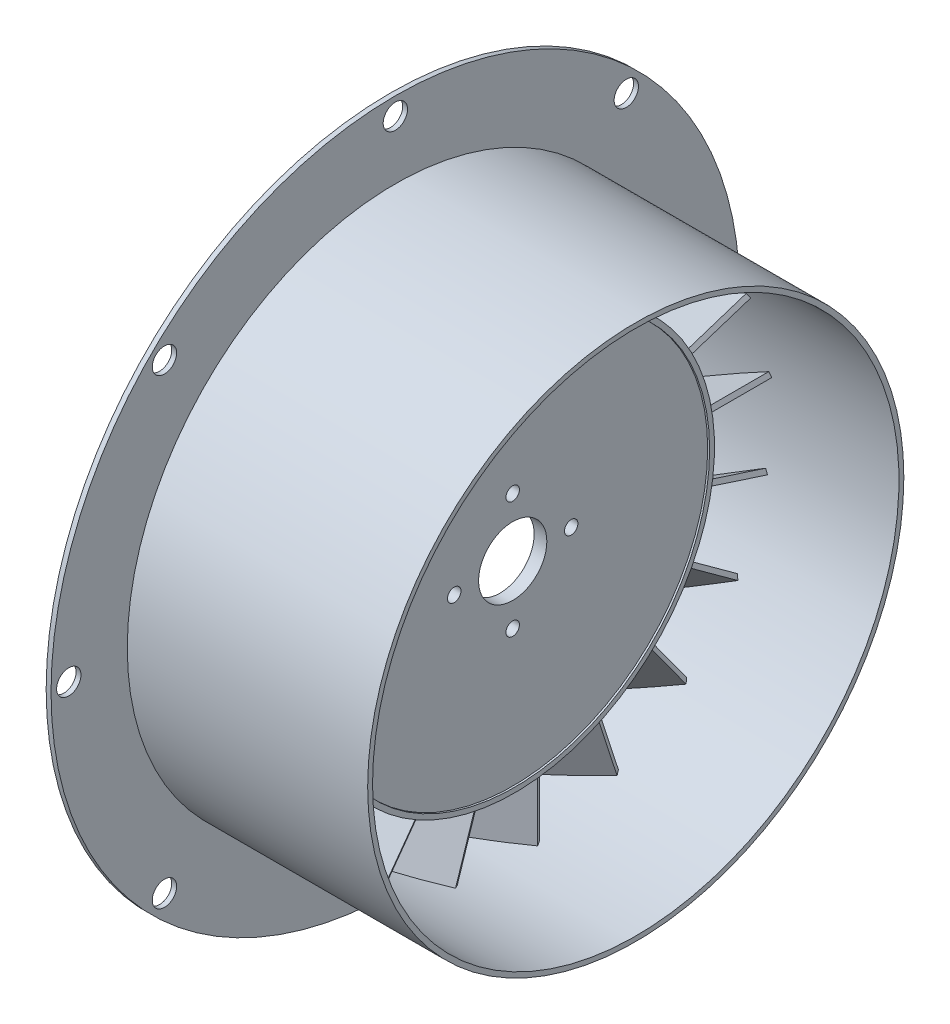
SolidWorks part; units mm, degrees
ref_plane "Front Plane" through (0, 0, 0) normal (0, 0, 1) x (1, 0, 0)
ref_plane "Top Plane" through (0, 0, 0) normal (0, 1, 0) x (1, 0, 0)
ref_plane "Right Plane" through (0, 0, 0) normal (1, 0, 0) x (0, 0, -1)
sketch "Sketch1" plane through (0, 0, 0) normal (0, 1, 0) x (1, 0, 0)
  line L0 (3.302, 0) -> (3.302, 50.8)
  line L1 (3.302, 50.8) -> (3.81, 50.8)
  line L2 (3.81, 50.8) -> (3.81, 52.07)
  line L3 (3.81, 52.07) -> (-25.4, 52.07)
  line L4 (-25.4, 52.07) -> (-25.4, 50.8)
  line L5 (-25.4, 50.8) -> (0, 50.8)
  line L6 (0, 50.8) -> (0, 0)
  line L7 (0, 0) -> (3.302, 0)
  dimension "D1" = 3.302
  dimension "D2" = 1.27
  dimension "D3" = 50.8
  dimension "D4" = 29.21
  dimension "D5" = 25.4
revolve "Revolve1" add sketch "Sketch1" angle 360 about L7
ref_plane "Plane1" through (0, 0, 83.82) normal (0, 0, 1) x (1, 0, 0)
sketch "Sketch2" plane through (0, 0, 83.82) normal (0, 0, 1) x (1, 0, 0)
  line L0 (-24.3107, 7.0701) -> (2.0857, -8.1699)
  line L1 (2.0857, -8.1699) -> (2.7207, -7.0701)
  line L3 (2.7207, -7.0701) -> (-23.6757, 8.1699)
  line L4 (-23.6757, 8.1699) -> (-24.3107, 7.0701)
  line L5 (-25.4, 0) -> (3.81, 0) construction
  line L6 (-25.4, 52.07) -> (-25.4, -52.07) construction
  line L7 (3.81, -52.07) -> (3.81, 52.07) construction
  line L8 (-11.1125, -0.5499) -> (-10.4775, 0.5499) construction
  point P4 (-10.795, 0)
  point P13 (-10.795, 0)
  dimension "D1" = 1.27
  dimension "D2" = 30
  dimension "D3" = 30.48
extrude "Boss-Extrude1" add sketch "Sketch2" along normal blind 16.51 from surface starting at face at (-25.4, 0, 52.07)
pattern_circular "CirPattern15" count 20 over 360 about axis through (0, 0, 0) along (1, 0, 0) of "Boss-Extrude1"
sketch "Sketch7" plane through (3.302, 0, 0) normal (1, 0, 0) x (0, 0, -1)
  circle A0 centre (0, 15.24) radius 1.7526
  circle A1 centre (0, 0) radius 8.89
  circle A2 centre (15.24, 0) radius 1.7526
  circle A3 centre (0, -15.24) radius 1.7526
  circle A4 centre (-15.24, 0) radius 1.7526
  point P14 (0, 0)
  dimension "D1" = 3.5052
  dimension "D3" = 17.78
  dimension "D2" = 15.24
  dimension "D4" = 4
extrude "Cut-Extrude1" cut sketch "Sketch7" against normal through all
sketch "Sketch8" plane through (0, 0, 0) normal (0, 0, 1) x (1, 0, 0)
  line L0 (35.3606, 69.85) -> (35.3606, 68.58)
  line L1 (35.3606, 68.58) -> (-28.5393, 68.58)
  line L2 (-28.5393, -76.2) -> (-28.5393, 76.2) construction
  line L3 (-28.5393, 68.58) -> (-28.5393, 89.7168)
  line L5 (-28.5393, 89.7168) -> (-27.2693, 89.7168)
  line L6 (-27.2693, 89.7168) -> (-27.2693, 69.85)
  line L7 (-27.2693, 69.85) -> (35.3606, 69.85)
  line L8 (35.3606, -69.85) -> (35.3606, 69.85) construction
  line L9 (-93.6879, 0) -> (-7.1026, 0) construction
  line L10 (0, 0) -> (79.505, 0) construction
  dimension "D1" = 68.58
  dimension "D2" = 1.27
  dimension "D3" = 1.27
revolve "Revolve2" add sketch "Sketch8" angle 360 about L10
sketch "Sketch9" plane through (-27.2693, 0, 0) normal (1, 0, 0) x (0, 0, -1)
  circle A0 centre (0, 85.09) radius 3.175
  circle A1 centre (60.1677, 60.1677) radius 3.175
  circle A2 centre (85.09, 0) radius 3.175
  circle A3 centre (60.1677, -60.1677) radius 3.175
  circle A4 centre (0, -85.09) radius 3.175
  circle A5 centre (-60.1677, -60.1677) radius 3.175
  circle A6 centre (-85.09, 0) radius 3.175
  circle A7 centre (-60.1677, 60.1677) radius 3.175
  point P19 (0, 0)
  dimension "D1" = 6.35
  dimension "D2" = 85.09
  dimension "D3" = 8
extrude "Cut-Extrude2" cut sketch "Sketch9" against normal blind 2.54
